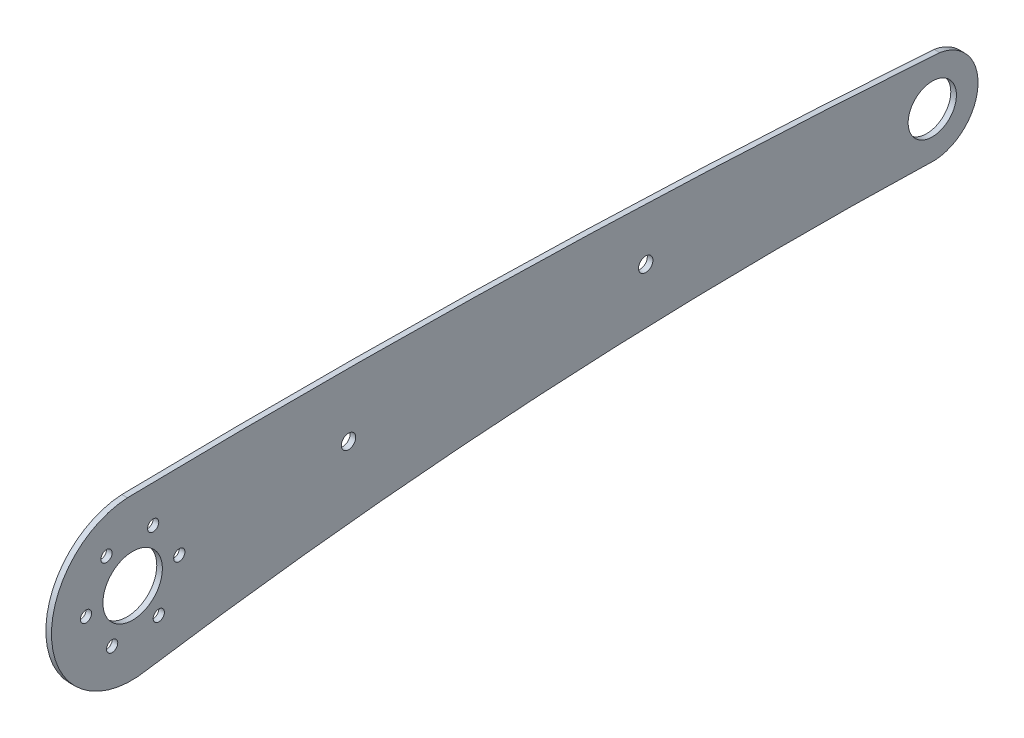
SolidWorks part; units mm, degrees
ref_plane "前基準面" through (0, 0, 0) normal (0, 0, 1) x (1, 0, 0)
ref_plane "上基準面" through (0, 0, 0) normal (0, 1, 0) x (1, 0, 0)
ref_plane "右基準面" through (0, 0, 0) normal (1, 0, 0) x (0, 0, -1)
sketch "草圖1" plane through (0, 0, 0) normal (1, 0, 0) x (0, 0, -1)
  circle A0 centre (-109.1339, 10.4963) radius 1.5
  circle A1 centre (-114.6135, -0.7386) radius 1.5
  circle A2 centre (-107.6236, -11.1016) radius 1.5
  circle A3 centre (-95.1541, -10.2296) radius 1.5
  circle A4 centre (-89.6744, 1.0053) radius 1.5
  circle A5 centre (-96.6643, 11.3683) radius 1.5
  circle A6 centre (111.6053, 3.6213) radius 6.45
  circle A7 centre (-102.144, 0.1333) radius 7.95
  circle A8 centre (35.0011, 5.9829) radius 1.925
  circle A9 centre (-44.4328, 4.6867) radius 1.925
  arc A10 (111.556, -8.572) -> (-98.2301, -21.2449) centre (76.1692, -1165.5062) ccw
  arc A11 (-103.5418, 21.202) -> (-98.2301, -21.2449) centre (-102.3984, -0.2107) ccw
  arc A12 (111.556, -8.572) -> (112.407, -8.5887) centre (112.0794, -3.5995) ccw
  arc A13 (112.407, -8.5887) -> (113.5845, 15.6966) centre (111.6053, 3.6213) ccw
  arc A14 (113.5845, 15.6966) -> (-103.5418, 21.202) centre (-56.6324, -2413.0729) ccw
extrude "填料-伸長1" add sketch "草圖1" along normal blind 1.5
